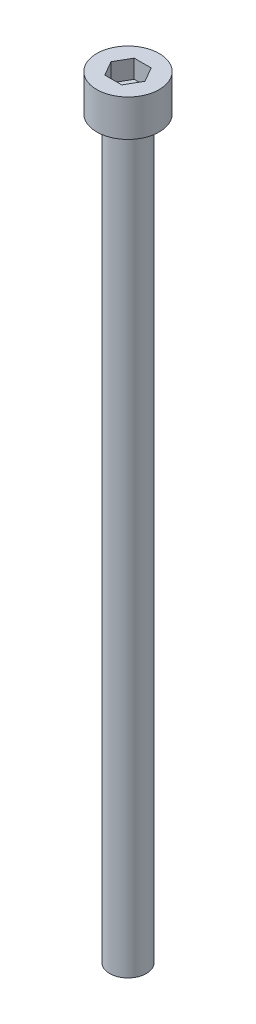
SolidWorks part; units mm, degrees
material "AISI 304"
ref_plane "前视基准面" through (0, 0, 0) normal (0, 0, 1) x (1, 0, 0)
ref_plane "上视基准面" through (0, 0, 0) normal (0, 1, 0) x (1, 0, 0)
ref_plane "右视基准面" through (0, 0, 0) normal (1, 0, 0) x (0, 0, -1)
sketch "草图1" plane through (0, 0, 0) normal (0, 1, 0) x (1, 0, 0)
  circle A0 centre (0, 0) radius 4.25
  dimension "D1" = 8.5
extrude "凸台-拉伸1" add sketch "草图1" along normal blind 5
sketch "草图2" plane through (0, 5, 0) normal (0, 1, 0) x (1, 0, 0)
  line L1 (2.3094, 0) -> (1.1547, 2)
  line L2 (1.1547, 2) -> (-1.1547, 2)
  line L3 (-1.1547, 2) -> (-2.3094, 0)
  line L4 (-2.3094, 0) -> (-1.1547, -2)
  line L5 (-1.1547, -2) -> (1.1547, -2)
  line L6 (1.1547, -2) -> (2.3094, 0)
  circle A0 centre (0, 0) radius 2 construction
  dimension "D1" = 4
extrude "切除-拉伸1" cut sketch "草图2" against normal blind 2.5
sketch "草图3" plane through (0, 0, 0) normal (0, -1, 0) x (1, 0, 0)
  circle A0 centre (0, 0) radius 2.5
  dimension "D1" = 5
extrude "凸台-拉伸2" add sketch "草图3" along normal blind 100
